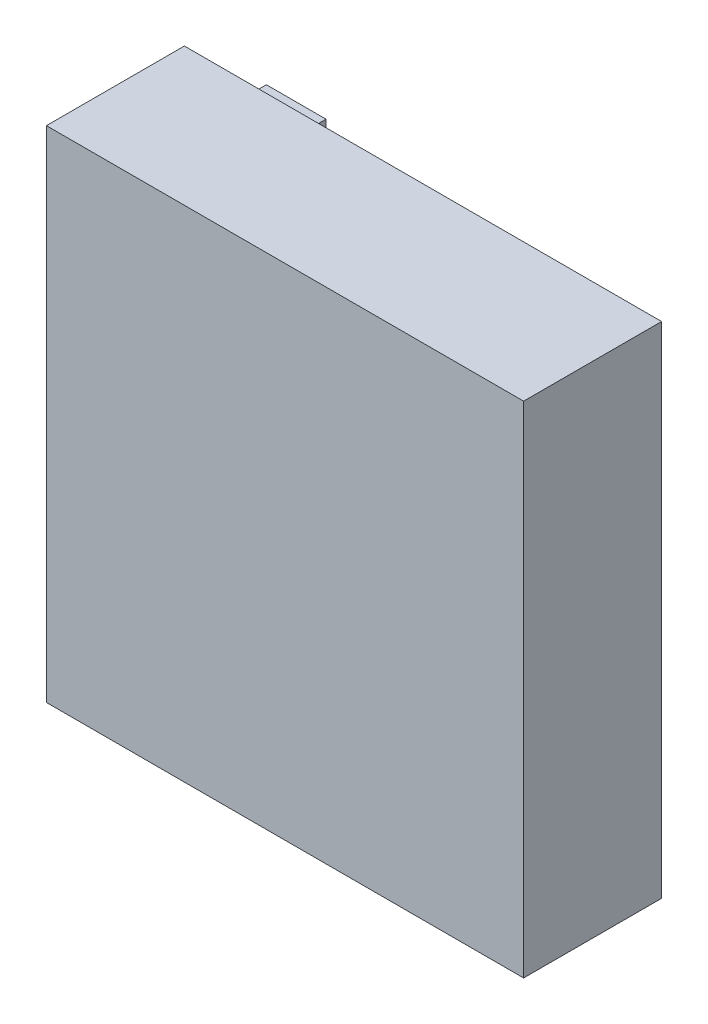
SolidWorks part; units mm, degrees
ref_plane "Plan de face" through (0, 0, 0) normal (0, 0, 1) x (1, 0, 0)
ref_plane "Plan de dessus" through (0, 0, 0) normal (0, 1, 0) x (1, 0, 0)
ref_plane "Plan de droite" through (0, 0, 0) normal (1, 0, 0) x (0, 0, -1)
sketch "Esquisse1" plane through (0, 0, 0) normal (0, 0, 1) x (1, 0, 0)
  line L1 (32, -33.5) -> (-32, -33.5)
  line L2 (32, -33.5) -> (32, 33.5)
  line L3 (32, 33.5) -> (-32, 33.5)
  line L4 (-32, -33.5) -> (-32, 33.5)
  line L5 (32, -33.5) -> (-32, 33.5) construction
  line L6 (32, 33.5) -> (-32, -33.5) construction
  point P0 (0, 0)
  dimension "D1" = 67
  dimension "D2" = 64
extrude "Boss.-Extru.1" add sketch "Esquisse1" along normal blind 18.5
sketch "Esquisse2" plane through (0, 0, 0) normal (0, 0, -1) x (-1, 0, 0)
  line L0 (32, 33.5) -> (32, -33.5) construction
  line L1 (25, 30.5) -> (17, 30.5)
  line L2 (25, 30.5) -> (25, 26.5)
  line L3 (25, 26.5) -> (17, 26.5)
  line L4 (17, 30.5) -> (17, 26.5)
  line L5 (25, 30.5) -> (17, 26.5) construction
  line L6 (25, 26.5) -> (17, 30.5) construction
  line L7 (-32, 33.5) -> (32, 33.5) construction
  point P0 (21, 28.5)
  dimension "D1" = 4
  dimension "D2" = 8
  dimension "D3" = 7
  dimension "D4" = 3
extrude "Boss.-Extru.2" add sketch "Esquisse2" along normal blind 4
